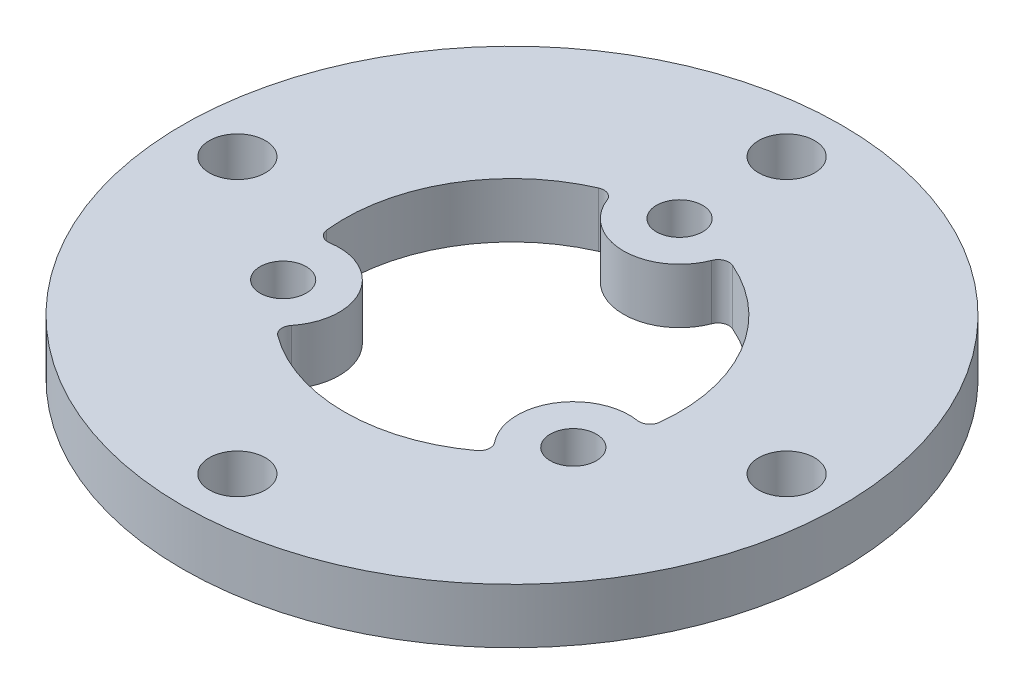
SolidWorks part; units mm, degrees
ref_plane "Front Plane" through (0, 0, 0) normal (0, 0, 1) x (1, 0, 0)
ref_plane "Top Plane" through (0, 0, 0) normal (0, 1, 0) x (1, 0, 0)
ref_plane "Right Plane" through (0, 0, 0) normal (1, 0, 0) x (0, 0, -1)
sketch "Sketch1" plane through (0, 0, 0) normal (0, 1, 0) x (1, 0, 0)
  circle A0 centre (0, 0) radius 10
  circle A1 centre (0, 0) radius 30
  circle A2 centre (0, 0) radius 15.25 construction
  circle A3 centre (0, 15.25) radius 2.1
  circle A6 centre (13.2069, -7.625) radius 2.1
  circle A7 centre (-13.2069, -7.625) radius 2.1
  circle A8 centre (0, 0) radius 25 construction
  circle A9 centre (0, 25) radius 2.55
  circle A10 centre (25, 0) radius 2.55
  circle A11 centre (0, -25) radius 2.55
  circle A12 centre (-25, 0) radius 2.55
  point P13 (0, 0)
  point P15 (-29.913, -2.2826)
  point P16 (0, 0)
  point P17 (0, 0)
  point P24 (0, 0)
  point P25 (0, 0)
  dimension "D1" = 20
  dimension "D2" = 60
  dimension "D3" = 30.5
  dimension "D4" = 4.2
  dimension "D6" = 5.1
  dimension "D7" = 50
  dimension "D5" = 3
  dimension "D8" = 4
extrude "Boss-Extrude1" add sketch "Sketch1" along normal blind 5
sketch "Sketch2" plane through (0, 5, 0) normal (0, 1, 0) x (1, 0, 0)
  arc A0 (-5.0282, 14.3972) -> (5.0282, 14.3972) centre (0, 15.25) ccw
  arc A1 (14.9825, -2.8441) -> (9.9543, -11.5532) centre (13.2069, -7.625) ccw
  arc A2 (-9.9543, -11.5532) -> (-14.9825, -2.8441) centre (-13.2069, -7.625) ccw
  arc A3 (-5.0282, 14.3972) -> (-14.9825, -2.8441) centre (0, 0) ccw
  arc A4 (-9.9543, -11.5532) -> (9.9543, -11.5532) centre (0, 0) ccw
  arc A5 (14.9825, -2.8441) -> (5.0282, 14.3972) centre (0, 0) ccw
  circle A6 centre (-13.2069, -7.625) radius 2.1 construction
  dimension "D1" = 3
extrude "Cut-Extrude1" cut sketch "Sketch2" against normal through all
fillet "Fillet1" radius 1 6 edges at (14.9825, 2.5, 2.8441) (9.9543, 2.5, 11.5532) (-9.9543, 2.5, 11.5532) (-14.9825, 2.5, 2.8441) (5.0282, 2.5, -14.3972) (-5.0282, 2.5, -14.3972)
